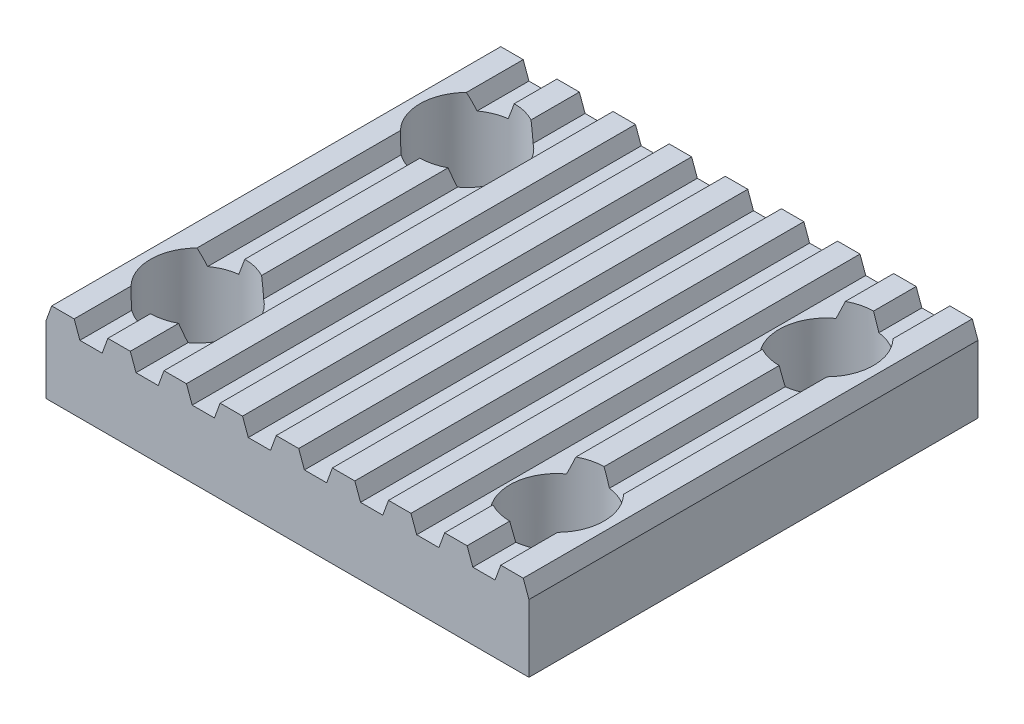
SolidWorks part; units mm, degrees
ref_plane "Front Plane" through (0, 0, 0) normal (0, 0, 1) x (1, 0, 0)
ref_plane "Top Plane" through (0, 0, 0) normal (0, 1, 0) x (1, 0, 0)
ref_plane "Right Plane" through (0, 0, 0) normal (1, 0, 0) x (0, 0, -1)
sketch "Sketch1" plane through (0, 0, 0) normal (0, 0, 1) x (1, 0, 0)
  line L0 (-10.7548, 1.5) -> (-10.5, 2.2)
  line L1 (10.7548, -1.5) -> (-10.7548, -1.5)
  line L4 (-10.7548, -1.5) -> (-10.7548, 1.5)
  line L5 (-10.7548, 1.5) -> (10.7548, -1.5) construction
  line L6 (10.7548, 1.5) -> (-10.7548, -1.5) construction
  line L7 (-10.5, 2.2) -> (-9.5, 2.2)
  line L8 (-9.5, 2.2) -> (-9.2452, 1.5)
  line L9 (-10.7548, 1.5) -> (-9.2452, 1.5) construction
  line L13 (-10, 1.5) -> (-10, 2.2) construction
  line L32 (10.7548, 1.5) -> (10.7548, -1.5)
  line L33 (-8, 2.2) -> (-7, 2.2)
  line L34 (-8.2548, 1.5) -> (-8, 2.2)
  line L35 (-7, 2.2) -> (-6.7452, 1.5)
  line L36 (-5.5, 2.2) -> (-4.5, 2.2)
  line L37 (-5.7548, 1.5) -> (-5.5, 2.2)
  line L38 (-4.5, 2.2) -> (-4.2452, 1.5)
  line L39 (-3, 2.2) -> (-2, 2.2)
  line L40 (-3.2548, 1.5) -> (-3, 2.2)
  line L41 (-2, 2.2) -> (-1.7452, 1.5)
  line L42 (-0.5, 2.2) -> (0.5, 2.2)
  line L43 (-0.7548, 1.5) -> (-0.5, 2.2)
  line L44 (0.5, 2.2) -> (0.7548, 1.5)
  line L45 (2, 2.2) -> (3, 2.2)
  line L46 (1.7452, 1.5) -> (2, 2.2)
  line L47 (3, 2.2) -> (3.2548, 1.5)
  line L48 (4.5, 2.2) -> (5.5, 2.2)
  line L49 (4.2452, 1.5) -> (4.5, 2.2)
  line L50 (5.5, 2.2) -> (5.7548, 1.5)
  line L51 (7, 2.2) -> (8, 2.2)
  line L52 (6.7452, 1.5) -> (7, 2.2)
  line L53 (8, 2.2) -> (8.2548, 1.5)
  line L54 (9.5, 2.2) -> (10.5, 2.2)
  line L55 (9.2452, 1.5) -> (9.5, 2.2)
  line L56 (10.5, 2.2) -> (10.7548, 1.5)
  line L60 (-9.2452, 1.5) -> (-8.2548, 1.5)
  line L61 (-6.7452, 1.5) -> (-5.7548, 1.5)
  line L62 (-4.2452, 1.5) -> (-3.2548, 1.5)
  line L63 (-1.7452, 1.5) -> (-0.7548, 1.5)
  line L64 (0.7548, 1.5) -> (1.7452, 1.5)
  line L65 (3.2548, 1.5) -> (4.2452, 1.5)
  line L66 (5.7548, 1.5) -> (6.7452, 1.5)
  line L67 (8.2548, 1.5) -> (9.2452, 1.5)
  line L70 (13.2548, 1.5) -> (14.2452, 1.5) [skipped]
  line L71 (11.7452, 1.5) -> (12, 2.2) [skipped]
  line L72 (12, 2.2) -> (13, 2.2) [skipped]
  line L73 (13, 2.2) -> (13.2548, 1.5) [skipped]
  line L74 (10.7548, 1.5) -> (11.7452, 1.5) [skipped]
  point P0 (0, 0)
  point P2 (0, 0)
  dimension "D1" = 3
  dimension "D2" = 3.7
  dimension "D3" = 40
  dimension "D4" = 1
  dimension "D5" = 10
  dimension "D6" = 10
extrude "Boss-Extrude1" add sketch "Sketch1" along normal mid plane 20
sketch "Sketch2" plane through (0, -1.5, 0) normal (0, -1, 0) x (1, 0, 0)
  line L0 (-11.516, 0) -> (10.7548, 0) construction
  line L1 (2.035, 0) -> (-2.035, 0) construction
  line L2 (10.7548, 10) -> (10.7548, -10) construction
  line L3 (0, 10) -> (0, -10) construction
  line L4 (-10.7548, 10) -> (10.7548, 10) construction
  line L5 (-10.7548, -10) -> (10.7548, -10) construction
  circle A0 centre (-8, -6) radius 2.1
  circle A1 centre (8, -6) radius 2.1
  circle A2 centre (8, 6) radius 2.1
  circle A3 centre (-8, 6) radius 2.1
  dimension "D1" = 16
  dimension "D2" = 12
  dimension "D3" = 4.2
extrude "Cut-Extrude1" cut sketch "Sketch2" against normal through all
